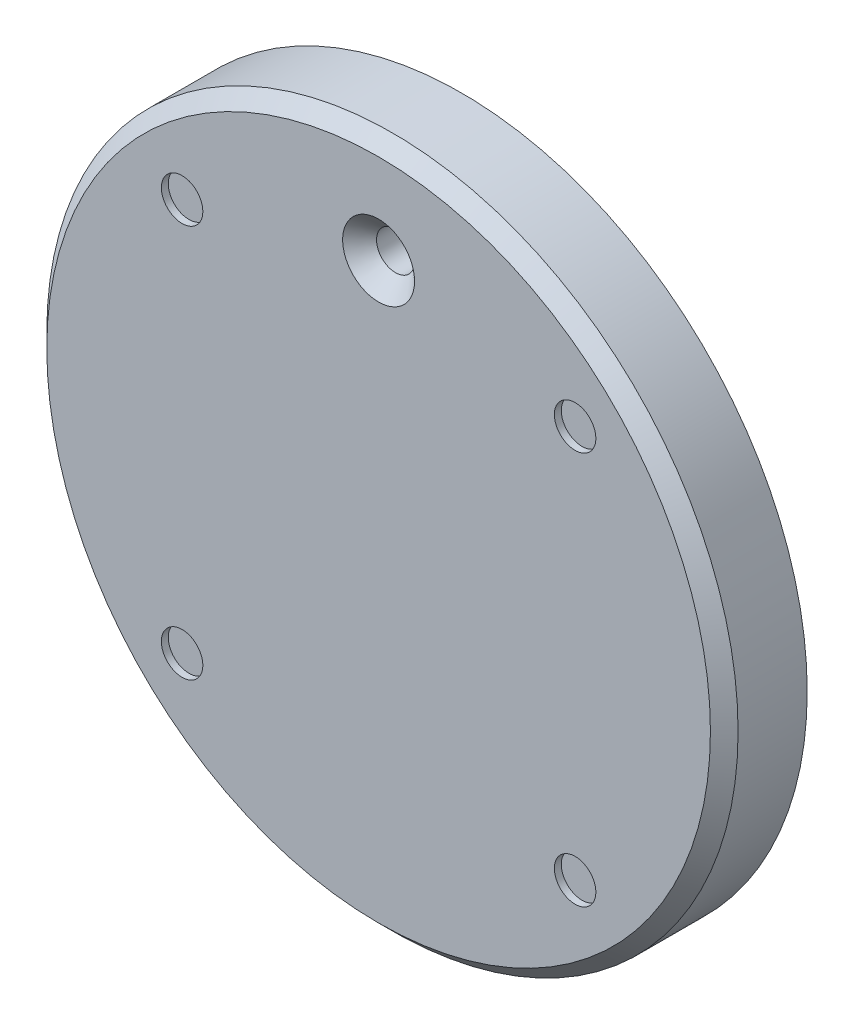
SolidWorks part; units mm, degrees
material "Oak"
ref_plane "Front Plane" through (0, 0, 0) normal (0, 0, 1) x (1, 0, 0)
ref_plane "Top Plane" through (0, 0, 0) normal (0, 1, 0) x (1, 0, 0)
ref_plane "Right Plane" through (0, 0, 0) normal (1, 0, 0) x (0, 0, -1)
sketch "Sketch2" plane through (0, 0, 0) normal (0, 0, 1) x (1, 0, 0)
  circle A0 centre (0, 0) radius 50
  dimension "D1" = 100
extrude "Boss-Extrude1" add sketch "Sketch2" along normal blind 12
sketch "Sketch4" plane through (0, 0, 12) normal (0, 0, 1) x (1, 0, 0)
  point P0 (0, 35)
  dimension "D1" = 35
hole_wizard "CSK for M5 Flat Head Machine Screw1" positions "Sketch4" profile "Sketch5" countersink size "M5" standard "ANSI Metric" end condition up to next
sketch "Sketch5" plane through (0, 35, 12) normal (1, 0, 0) x (0, -1, 0)
  line L0 (0, 0) -> (0, 12)
  line L1 (0, 12) -> (2.75, 12)
  line L2 (2.75, 12) -> (2.75, 2.45)
  line L3 (2.75, 2.45) -> (5.2, 0)
  line L5 (5.2, 0) -> (0, 0)
  line L6 (-2.75, 2.45) -> (-5.2, 0) construction
  line L11 (0, -6.35) -> (0, 107.95) construction
  dimension "Thru Hole Dia." = 5.5
  dimension "Thru Hole Depth" = 12
  dimension "Near C'Sink Dia." = 10.4
  dimension "Near C'Sink Angle" = 90
sketch "Sketch6" plane through (0, 0, 12) normal (0, 0, 1) x (1, 0, 0)
  circle A0 centre (0, 0) radius 40.2 construction
  circle A1 centre (0, 35) radius 5.2 construction
  circle A2 centre (-28.4257, 28.4257) radius 3
  circle A3 centre (28.4257, 28.4257) radius 3
  circle A4 centre (28.4257, -28.4257) radius 3
  circle A5 centre (-28.4257, -28.4257) radius 3
  point P17 (0, 0)
  dimension "D1" = 6
  dimension "D2" = 4
extrude "Cut-Extrude1" cut sketch "Sketch6" against normal blind 1
chamfer "Chamfer1" distance 2 angle 45 1 edges at (50, 0, 12)
